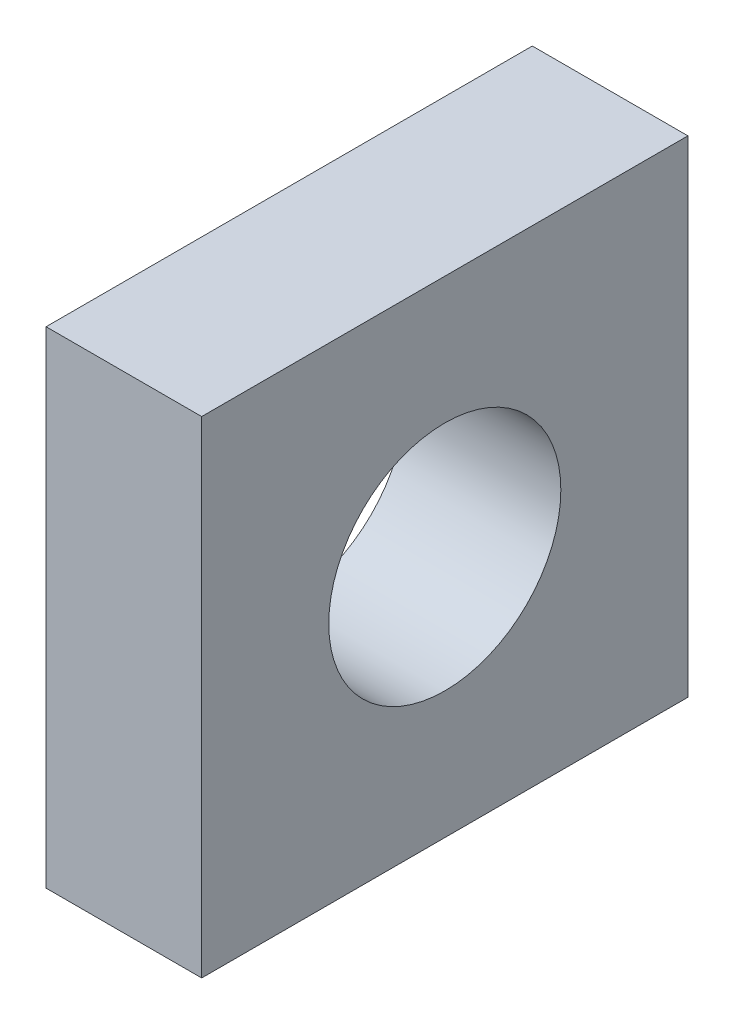
SolidWorks part; units mm, degrees
ref_plane "Front Plane" through (0, 0, 0) normal (0, 0, 1) x (1, 0, 0)
ref_plane "Top Plane" through (0, 0, 0) normal (0, 1, 0) x (1, 0, 0)
ref_plane "Right Plane" through (0, 0, 0) normal (1, 0, 0) x (0, 0, -1)
ref_plane "Plane1" through (3.4, 0, 0) normal (-1, 0, 0) x (0, -1, 0)
sketch "Sketch1" plane through (3.4, 0, 0) normal (-1, 0, 0) x (0, -1, 0)
  line L0 (-9, 29) -> (-9, 39)
  line L1 (-9, 39) -> (-19, 39)
  line L2 (-19, 39) -> (-19, 29)
  line L3 (-19, 29) -> (-9, 29)
  circle A0 centre (-14, 34) radius 2.3866
extrude "Boss-Extrude1" add sketch "Sketch1" against normal blind 3.2
